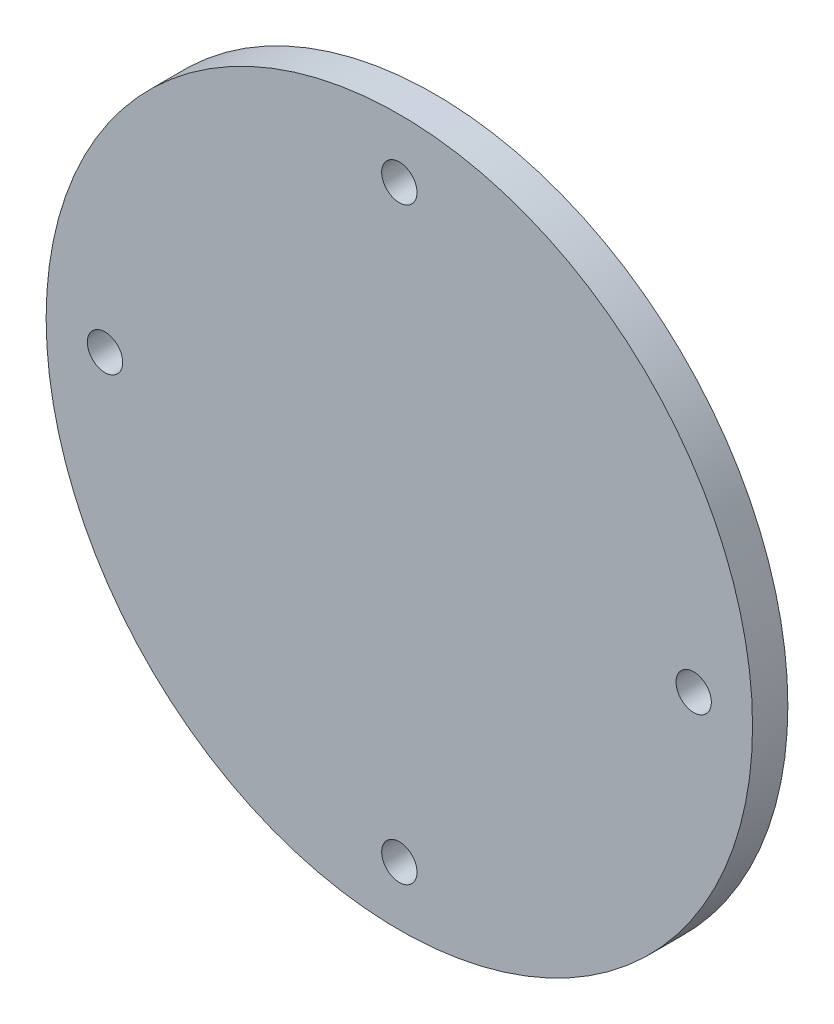
SolidWorks part; units mm, degrees
ref_plane "Plan de face" through (0, 0, 0) normal (0, 0, 1) x (1, 0, 0)
ref_plane "Plan de dessus" through (0, 0, 0) normal (0, 1, 0) x (1, 0, 0)
ref_plane "Plan de droite" through (0, 0, 0) normal (1, 0, 0) x (0, 0, -1)
sketch "Esquisse1" plane through (0, 0, 0) normal (0, 0, 1) x (1, 0, 0)
  line L0 (0, 25) -> (0, -25) construction
  line L1 (-25, 0) -> (25, 0) construction
  circle A0 centre (0, 0) radius 25
  circle A1 centre (0, 0) radius 30
  circle A6 centre (0, 25) radius 1.5
  circle A7 centre (-25, 0) radius 1.5
  circle A8 centre (25, 0) radius 1.5
  circle A9 centre (0, -25) radius 1.5
  dimension "D1" = 60
  dimension "D2" = 50
  dimension "D3" = 3
  dimension "D4" = 3
  dimension "D5" = 3
  dimension "D6" = 3
extrude "Boss.-Extru.1" add sketch "Esquisse1" along normal blind 3 contours A9 A0 A8 A6 A7 | A1 A9 A0 A7 A6 A8
